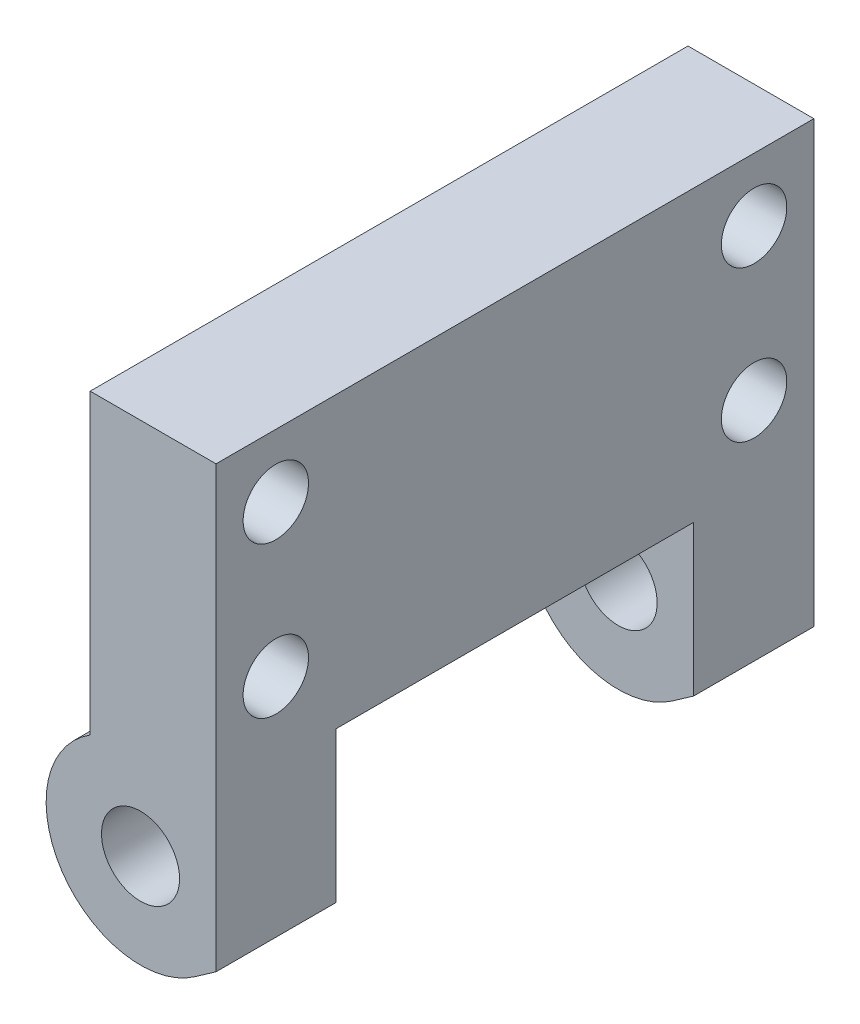
SolidWorks part; units mm, degrees
ref_plane "Front Plane" through (0, 0, 0) normal (0, 0, 1) x (1, 0, 0)
ref_plane "Top Plane" through (0, 0, 0) normal (0, 1, 0) x (1, 0, 0)
ref_plane "Right Plane" through (0, 0, 0) normal (1, 0, 0) x (0, 0, -1)
sketch "Sketch1" plane through (0, 0, 0) normal (0, 0, 1) x (1, 0, 0)
  line L0 (-4, 6.3443) -> (-4, 30)
  line L1 (-4, 30) -> (6, 30)
  line L2 (6, 30) -> (6, -4.9546)
  line L3 (4.3018, -6.1436) -> (6, -4.9546)
  line L4 (6, -4.9546) -> (-1.2144, -4.9546) construction
  circle A0 centre (0, 0) radius 3.1
  arc A1 (-4, 6.3443) -> (4.3018, -6.1436) centre (0, 0) ccw
  dimension "D1" = 15
  dimension "D2" = 6.2
  dimension "D3" = 30
  dimension "D4" = 4
  dimension "D5" = 6
  dimension "D6" = 35
extrude "Boss-Extrude1" add sketch "Sketch1" along normal blind 47.5
sketch "Sketch2" plane through (6, 0, 0) normal (1, 0, 0) x (0, 0, -1)
  line L0 (-23.75, 7) -> (-23.75, 30) construction
  line L1 (-37.95, 7) -> (-9.55, 7)
  line L2 (-37.95, 7) -> (-37.95, -11.0327)
  line L3 (-37.95, -11.0327) -> (-9.55, -11.0327)
  line L4 (-9.55, 7) -> (-9.55, -11.0327)
  line L5 (-47.5, 30) -> (0, 30) construction
  dimension "D1" = 7
  dimension "D2" = 28.4
extrude "Cut-Extrude1" cut sketch "Sketch2" against normal through all
sketch "Sketch3" plane through (-4, 0, 0) normal (-1, 0, 0) x (0, 0, 1)
  line L1 (47.5, 30) -> (0, 30) construction
  line L3 (23.75, 30) -> (23.75, 7) construction
  line L4 (9.55, 7) -> (37.95, 7) construction
  circle A0 centre (4.75, 25) radius 2.6
  circle A1 centre (4.75, 13) radius 2.6
  circle A2 centre (42.75, 25) radius 2.6
  circle A3 centre (42.75, 13) radius 2.6
  dimension "D1" = 5.2
  dimension "D2" = 19
  dimension "D3" = 5
  dimension "D4" = 12
  dimension "D5" = 19
extrude "Cut-Extrude2" cut sketch "Sketch3" against normal through all
